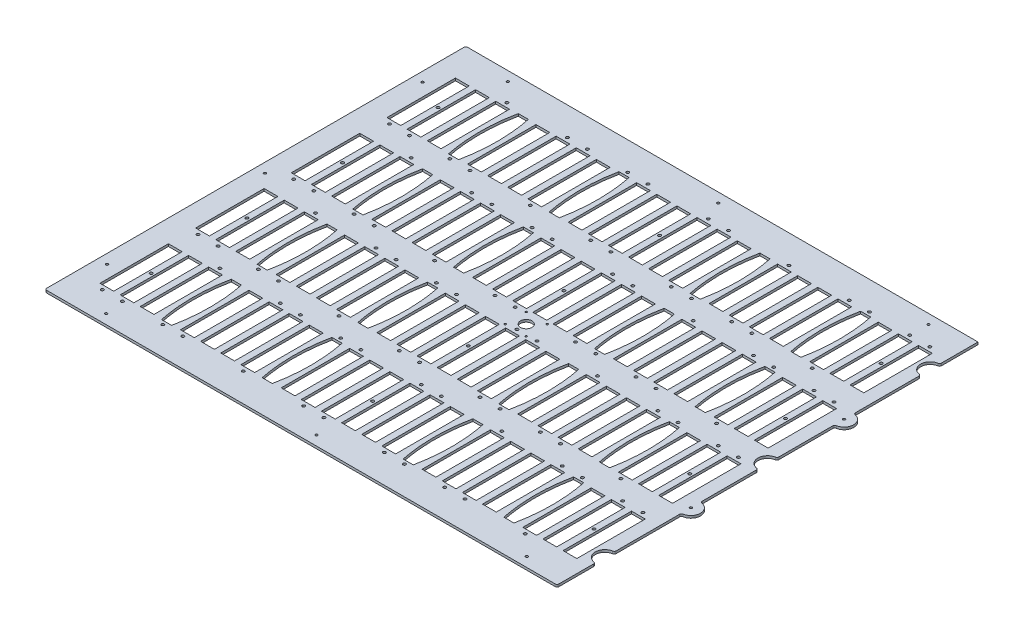
SolidWorks part; units mm, degrees
ref_plane "Front Plane" through (0, 0, 0) normal (0, 0, 1) x (1, 0, 0)
ref_plane "Top Plane" through (0, 0, 0) normal (0, 1, 0) x (1, 0, 0)
ref_plane "Right Plane" through (0, 0, 0) normal (1, 0, 0) x (0, 0, -1)
sketch "Sketch1" plane through (0, 0, 0) normal (0, 1, 0) x (1, 0, 0)
  line L0 (-340.1822, 0) -> (340.1822, 0) construction
  line L1 (-340.1822, -279.5524) -> (340.1822, -279.5524)
  line L2 (-340.1822, -279.5524) -> (-340.1822, 279.5524)
  line L3 (-340.1822, 279.5524) -> (340.1822, 279.5524)
  line L4 (340.1822, -279.5524) -> (340.1822, -228.7524)
  line L5 (-340.1822, -279.5524) -> (340.1822, 279.5524) construction
  line L6 (-340.1822, 279.5524) -> (340.1822, -279.5524) construction
  line L7 (340.1822, -89.0524) -> (340.1822, -12.7)
  line L8 (340.1822, -203.3524) -> (340.1822, -114.4524)
  line L9 (340.1822, 12.7) -> (340.1822, 89.0524)
  line L10 (340.1822, 114.4524) -> (340.1822, 203.3524)
  line L11 (340.1822, 228.7524) -> (340.1822, 279.5524)
  arc A0 (340.1822, 12.7) -> (340.1822, -12.7) centre (340.1822, 0) ccw
  arc A1 (340.1822, -114.4524) -> (340.1822, -89.0524) centre (340.1822, -101.7524) ccw
  arc A2 (340.1822, 89.0524) -> (340.1822, 114.4524) centre (340.1822, 101.7524) ccw
  arc A3 (340.1822, -203.3524) -> (340.1822, -228.7524) centre (340.1822, -216.0524) ccw
  arc A4 (340.1822, 228.7524) -> (340.1822, 203.3524) centre (340.1822, 216.0524) ccw
  point P0 (0, 0)
  dimension "D3" = 63.5
  dimension "D4" = 12.7
  dimension "D5" = 63.5
  dimension "D6" = 177.8
  dimension "D7" = 177.8
  dimension "D1" = 559.1048
  dimension "D2" = 680.3644
extrude "Boss-Extrude1" add sketch "Sketch1" along normal blind 3.175
sketch "Sketch17" plane through (0, 3.175, 0) normal (0, 1, 0) x (1, 0, 0)
  line L0 (340.1822, 279.5524) -> (-340.1822, 279.5524) construction
  line L1 (-314.7822, 254.1524) -> (327.4822, 254.1524) construction
  line L2 (-314.7822, 254.1524) -> (-314.7822, -254.1524) construction
  line L3 (-314.7822, -254.1524) -> (327.4822, -254.1524) construction
  line L4 (327.4822, 254.1524) -> (327.4822, -254.1524) construction
  line L5 (-340.1822, 279.5524) -> (-340.1822, -279.5524) construction
  line L6 (-340.1822, -279.5524) -> (340.1822, -279.5524) construction
  line L7 (340.1822, -203.3524) -> (340.1822, -114.4524) construction
  line L8 (-283.771, 236.1184) -> (-265.483, 236.1184)
  line L9 (-310.515, 236.1184) -> (-292.227, 236.1184)
  line L10 (-310.515, 236.1184) -> (-310.515, 145.1864)
  line L11 (-310.515, 145.1864) -> (-292.227, 145.1864)
  line L12 (-292.227, 236.1184) -> (-292.227, 145.1864)
  line L13 (-283.771, 236.1184) -> (-283.771, 145.1864)
  line L14 (-265.483, 236.1184) -> (-265.483, 145.1864)
  line L15 (-283.771, 145.1864) -> (-265.483, 145.1864)
  line L16 (-257.027, 236.1184) -> (-238.739, 236.1184)
  line L17 (-257.027, 236.1184) -> (-257.027, 145.1864)
  line L18 (-238.739, 236.1184) -> (-238.739, 145.1864)
  line L19 (-257.027, 145.1864) -> (-238.739, 145.1864)
  line L24 (-203.539, 236.1184) -> (-185.251, 236.1184)
  line L25 (-203.539, 236.1184) -> (-203.539, 145.1864)
  line L26 (-185.251, 236.1184) -> (-185.251, 145.1864)
  line L27 (-203.539, 145.1864) -> (-185.251, 145.1864)
  line L28 (-176.795, 236.1184) -> (-158.507, 236.1184)
  line L29 (-176.795, 236.1184) -> (-176.795, 145.1864)
  line L30 (-158.507, 236.1184) -> (-158.507, 145.1864)
  line L31 (-176.795, 145.1864) -> (-158.507, 145.1864)
  line L32 (-150.0511, 236.1184) -> (-131.7631, 236.1184)
  line L33 (-150.0511, 236.1184) -> (-150.0511, 145.1864)
  line L34 (-131.7631, 236.1184) -> (-131.7631, 145.1864)
  line L35 (-150.0511, 145.1864) -> (-131.7631, 145.1864)
  line L36 (-123.3071, 236.1184) -> (-105.0191, 236.1184)
  line L37 (-123.3071, 236.1184) -> (-123.3071, 145.1864)
  line L38 (-105.0191, 236.1184) -> (-105.0191, 145.1864)
  line L39 (-123.3071, 145.1864) -> (-105.0191, 145.1864)
  line L44 (-69.8191, 236.1184) -> (-51.5311, 236.1184)
  line L45 (-69.8191, 236.1184) -> (-69.8191, 145.1864)
  line L46 (-51.5311, 236.1184) -> (-51.5311, 145.1864)
  line L47 (-69.8191, 145.1864) -> (-51.5311, 145.1864)
  line L48 (-43.0751, 236.1184) -> (-24.7871, 236.1184)
  line L49 (-43.0751, 236.1184) -> (-43.0751, 145.1864)
  line L50 (-24.7871, 236.1184) -> (-24.7871, 145.1864)
  line L51 (-43.0751, 145.1864) -> (-24.7871, 145.1864)
  line L52 (-16.3311, 236.1184) -> (1.9569, 236.1184)
  line L53 (-16.3311, 236.1184) -> (-16.3311, 145.1864)
  line L54 (1.9569, 236.1184) -> (1.9569, 145.1864)
  line L55 (-16.3311, 145.1864) -> (1.9569, 145.1864)
  line L56 (10.4129, 236.1184) -> (28.7009, 236.1184)
  line L57 (10.4129, 236.1184) -> (10.4129, 145.1864)
  line L58 (28.7009, 236.1184) -> (28.7009, 145.1864)
  line L59 (10.4129, 145.1864) -> (28.7009, 145.1864)
  line L60 (37.1569, 236.1184) -> (55.4449, 236.1184)
  line L61 (37.1569, 236.1184) -> (37.1569, 145.1864)
  line L62 (55.4449, 236.1184) -> (55.4449, 145.1864)
  line L63 (37.1569, 145.1864) -> (55.4449, 145.1864)
  line L64 (63.9009, 236.1184) -> (82.1889, 236.1184)
  line L65 (63.9009, 236.1184) -> (63.9009, 145.1864)
  line L66 (82.1889, 236.1184) -> (82.1889, 145.1864)
  line L67 (63.9009, 145.1864) -> (82.1889, 145.1864)
  line L72 (117.3889, 236.1184) -> (135.6769, 236.1184)
  line L73 (117.3889, 236.1184) -> (117.3889, 145.1864)
  line L74 (135.6769, 236.1184) -> (135.6769, 145.1864)
  line L75 (117.3889, 145.1864) -> (135.6769, 145.1864)
  line L76 (144.1329, 236.1184) -> (162.4209, 236.1184)
  line L77 (144.1329, 236.1184) -> (144.1329, 145.1864)
  line L78 (162.4209, 236.1184) -> (162.4209, 145.1864)
  line L79 (144.1329, 145.1864) -> (162.4209, 145.1864)
  line L80 (170.8768, 236.1184) -> (189.1648, 236.1184)
  line L81 (170.8768, 236.1184) -> (170.8768, 145.1864)
  line L82 (189.1648, 236.1184) -> (189.1648, 145.1864)
  line L83 (170.8768, 145.1864) -> (189.1648, 145.1864)
  line L84 (197.6208, 236.1184) -> (215.9088, 236.1184)
  line L85 (197.6208, 236.1184) -> (197.6208, 145.1864)
  line L86 (215.9088, 236.1184) -> (215.9088, 145.1864)
  line L87 (197.6208, 145.1864) -> (215.9088, 145.1864)
  line L92 (251.1088, 236.1184) -> (269.3968, 236.1184)
  line L93 (251.1088, 236.1184) -> (251.1088, 145.1864)
  line L94 (269.3968, 236.1184) -> (269.3968, 145.1864)
  line L95 (251.1088, 145.1864) -> (269.3968, 145.1864)
  line L96 (277.8528, 236.1184) -> (296.1408, 236.1184)
  line L97 (277.8528, 236.1184) -> (277.8528, 145.1864)
  line L98 (296.1408, 236.1184) -> (296.1408, 145.1864)
  line L99 (277.8528, 145.1864) -> (296.1408, 145.1864)
  line L100 (304.5968, 236.1184) -> (322.8848, 236.1184)
  line L101 (304.5968, 236.1184) -> (304.5968, 145.1864)
  line L102 (322.8848, 236.1184) -> (322.8848, 145.1864)
  line L103 (304.5968, 145.1864) -> (322.8848, 145.1864)
  line L104 (-283.771, 109.0422) -> (-265.483, 109.0422)
  line L105 (-283.771, 109.0422) -> (-283.771, 18.1102)
  line L106 (-265.483, 109.0422) -> (-265.483, 18.1102)
  line L107 (-283.771, 18.1102) -> (-265.483, 18.1102)
  line L108 (-257.027, 109.0422) -> (-238.739, 109.0422)
  line L109 (-257.027, 109.0422) -> (-257.027, 18.1102)
  line L110 (-238.739, 109.0422) -> (-238.739, 18.1102)
  line L111 (-257.027, 18.1102) -> (-238.739, 18.1102)
  line L116 (-203.539, 109.0422) -> (-185.251, 109.0422)
  line L117 (-203.539, 109.0422) -> (-203.539, 18.1102)
  line L118 (-185.251, 109.0422) -> (-185.251, 18.1102)
  line L119 (-203.539, 18.1102) -> (-185.251, 18.1102)
  line L120 (-176.795, 109.0422) -> (-158.507, 109.0422)
  line L121 (-176.795, 109.0422) -> (-176.795, 18.1102)
  line L122 (-158.507, 109.0422) -> (-158.507, 18.1102)
  line L123 (-176.795, 18.1102) -> (-158.507, 18.1102)
  line L124 (-150.0511, 109.0422) -> (-131.7631, 109.0422)
  line L125 (-150.0511, 109.0422) -> (-150.0511, 18.1102)
  line L126 (-131.7631, 109.0422) -> (-131.7631, 18.1102)
  line L127 (-150.0511, 18.1102) -> (-131.7631, 18.1102)
  line L128 (-123.3071, 109.0422) -> (-105.0191, 109.0422)
  line L129 (-123.3071, 109.0422) -> (-123.3071, 18.1102)
  line L130 (-105.0191, 109.0422) -> (-105.0191, 18.1102)
  line L131 (-123.3071, 18.1102) -> (-105.0191, 18.1102)
  line L136 (-69.8191, 109.0422) -> (-51.5311, 109.0422)
  line L137 (-69.8191, 109.0422) -> (-69.8191, 18.1102)
  line L138 (-51.5311, 109.0422) -> (-51.5311, 18.1102)
  line L139 (-69.8191, 18.1102) -> (-51.5311, 18.1102)
  line L140 (-43.0751, 109.0422) -> (-24.7871, 109.0422)
  line L141 (-43.0751, 109.0422) -> (-43.0751, 18.1102)
  line L142 (-24.7871, 109.0422) -> (-24.7871, 18.1102)
  line L143 (-43.0751, 18.1102) -> (-24.7871, 18.1102)
  line L144 (-16.3311, 109.0422) -> (1.9569, 109.0422)
  line L145 (-16.3311, 109.0422) -> (-16.3311, 18.1102)
  line L146 (1.9569, 109.0422) -> (1.9569, 18.1102)
  line L147 (-16.3311, 18.1102) -> (1.9569, 18.1102)
  line L148 (10.4129, 109.0422) -> (28.7009, 109.0422)
  line L149 (10.4129, 109.0422) -> (10.4129, 18.1102)
  line L150 (28.7009, 109.0422) -> (28.7009, 18.1102)
  line L151 (10.4129, 18.1102) -> (28.7009, 18.1102)
  line L152 (37.1569, 109.0422) -> (55.4449, 109.0422)
  line L153 (37.1569, 109.0422) -> (37.1569, 18.1102)
  line L154 (55.4449, 109.0422) -> (55.4449, 18.1102)
  line L155 (37.1569, 18.1102) -> (55.4449, 18.1102)
  line L156 (63.9009, 109.0422) -> (82.1889, 109.0422)
  line L157 (63.9009, 109.0422) -> (63.9009, 18.1102)
  line L158 (82.1889, 109.0422) -> (82.1889, 18.1102)
  line L159 (63.9009, 18.1102) -> (82.1889, 18.1102)
  line L164 (117.3889, 109.0422) -> (135.6769, 109.0422)
  line L165 (117.3889, 109.0422) -> (117.3889, 18.1102)
  line L166 (135.6769, 109.0422) -> (135.6769, 18.1102)
  line L167 (117.3889, 18.1102) -> (135.6769, 18.1102)
  line L168 (144.1329, 109.0422) -> (162.4209, 109.0422)
  line L169 (144.1329, 109.0422) -> (144.1329, 18.1102)
  line L170 (162.4209, 109.0422) -> (162.4209, 18.1102)
  line L171 (144.1329, 18.1102) -> (162.4209, 18.1102)
  line L172 (170.8768, 109.0422) -> (189.1648, 109.0422)
  line L173 (170.8768, 109.0422) -> (170.8768, 18.1102)
  line L174 (189.1648, 109.0422) -> (189.1648, 18.1102)
  line L175 (170.8768, 18.1102) -> (189.1648, 18.1102)
  line L176 (197.6208, 109.0422) -> (215.9088, 109.0422)
  line L177 (197.6208, 109.0422) -> (197.6208, 18.1102)
  line L178 (215.9088, 109.0422) -> (215.9088, 18.1102)
  line L179 (197.6208, 18.1102) -> (215.9088, 18.1102)
  line L184 (251.1088, 109.0422) -> (269.3968, 109.0422)
  line L185 (251.1088, 109.0422) -> (251.1088, 18.1102)
  line L186 (269.3968, 109.0422) -> (269.3968, 18.1102)
  line L187 (251.1088, 18.1102) -> (269.3968, 18.1102)
  line L188 (277.8528, 109.0422) -> (296.1408, 109.0422)
  line L189 (277.8528, 109.0422) -> (277.8528, 18.1102)
  line L190 (296.1408, 109.0422) -> (296.1408, 18.1102)
  line L191 (277.8528, 18.1102) -> (296.1408, 18.1102)
  line L192 (304.5968, 109.0422) -> (322.8848, 109.0422)
  line L193 (304.5968, 109.0422) -> (304.5968, 18.1102)
  line L194 (322.8848, 109.0422) -> (322.8848, 18.1102)
  line L195 (304.5968, 18.1102) -> (322.8848, 18.1102)
  line L196 (-283.771, -18.034) -> (-265.483, -18.034)
  line L197 (-283.771, -18.034) -> (-283.771, -108.966)
  line L198 (-265.483, -18.034) -> (-265.483, -108.966)
  line L199 (-283.771, -108.966) -> (-265.483, -108.966)
  line L200 (-257.027, -18.034) -> (-238.739, -18.034)
  line L201 (-257.027, -18.034) -> (-257.027, -108.966)
  line L202 (-238.739, -18.034) -> (-238.739, -108.966)
  line L203 (-257.027, -108.966) -> (-238.739, -108.966)
  line L208 (-203.539, -18.034) -> (-185.251, -18.034)
  line L209 (-203.539, -18.034) -> (-203.539, -108.966)
  line L210 (-185.251, -18.034) -> (-185.251, -108.966)
  line L211 (-203.539, -108.966) -> (-185.251, -108.966)
  line L212 (-176.795, -18.034) -> (-158.507, -18.034)
  line L213 (-176.795, -18.034) -> (-176.795, -108.966)
  line L214 (-158.507, -18.034) -> (-158.507, -108.966)
  line L215 (-176.795, -108.966) -> (-158.507, -108.966)
  line L216 (-150.0511, -18.034) -> (-131.7631, -18.034)
  line L217 (-150.0511, -18.034) -> (-150.0511, -108.966)
  line L218 (-131.7631, -18.034) -> (-131.7631, -108.966)
  line L219 (-150.0511, -108.966) -> (-131.7631, -108.966)
  line L220 (-123.3071, -18.034) -> (-105.0191, -18.034)
  line L221 (-123.3071, -18.034) -> (-123.3071, -108.966)
  line L222 (-105.0191, -18.034) -> (-105.0191, -108.966)
  line L223 (-123.3071, -108.966) -> (-105.0191, -108.966)
  line L228 (-69.8191, -18.034) -> (-51.5311, -18.034)
  line L229 (-69.8191, -18.034) -> (-69.8191, -108.966)
  line L230 (-51.5311, -18.034) -> (-51.5311, -108.966)
  line L231 (-69.8191, -108.966) -> (-51.5311, -108.966)
  line L232 (-43.0751, -18.034) -> (-24.7871, -18.034)
  line L233 (-43.0751, -18.034) -> (-43.0751, -108.966)
  line L234 (-24.7871, -18.034) -> (-24.7871, -108.966)
  line L235 (-43.0751, -108.966) -> (-24.7871, -108.966)
  line L236 (-16.3311, -18.034) -> (1.9569, -18.034)
  line L237 (-16.3311, -18.034) -> (-16.3311, -108.966)
  line L238 (1.9569, -18.034) -> (1.9569, -108.966)
  line L239 (-16.3311, -108.966) -> (1.9569, -108.966)
  line L240 (10.4129, -18.034) -> (28.7009, -18.034)
  line L241 (10.4129, -18.034) -> (10.4129, -108.966)
  line L242 (28.7009, -18.034) -> (28.7009, -108.966)
  line L243 (10.4129, -108.966) -> (28.7009, -108.966)
  line L244 (37.1569, -18.034) -> (55.4449, -18.034)
  line L245 (37.1569, -18.034) -> (37.1569, -108.966)
  line L246 (55.4449, -18.034) -> (55.4449, -108.966)
  line L247 (37.1569, -108.966) -> (55.4449, -108.966)
  line L248 (63.9009, -18.034) -> (82.1889, -18.034)
  line L249 (63.9009, -18.034) -> (63.9009, -108.966)
  line L250 (82.1889, -18.034) -> (82.1889, -108.966)
  line L251 (63.9009, -108.966) -> (82.1889, -108.966)
  line L256 (117.3889, -18.034) -> (135.6769, -18.034)
  line L257 (117.3889, -18.034) -> (117.3889, -108.966)
  line L258 (135.6769, -18.034) -> (135.6769, -108.966)
  line L259 (117.3889, -108.966) -> (135.6769, -108.966)
  line L260 (144.1329, -18.034) -> (162.4209, -18.034)
  line L261 (144.1329, -18.034) -> (144.1329, -108.966)
  line L262 (162.4209, -18.034) -> (162.4209, -108.966)
  line L263 (144.1329, -108.966) -> (162.4209, -108.966)
  line L264 (170.8768, -18.034) -> (189.1648, -18.034)
  line L265 (170.8768, -18.034) -> (170.8768, -108.966)
  line L266 (189.1648, -18.034) -> (189.1648, -108.966)
  line L267 (170.8768, -108.966) -> (189.1648, -108.966)
  line L268 (197.6208, -18.034) -> (215.9088, -18.034)
  line L269 (197.6208, -18.034) -> (197.6208, -108.966)
  line L270 (215.9088, -18.034) -> (215.9088, -108.966)
  line L271 (197.6208, -108.966) -> (215.9088, -108.966)
  line L276 (251.1088, -18.034) -> (269.3968, -18.034)
  line L277 (251.1088, -18.034) -> (251.1088, -108.966)
  line L278 (269.3968, -18.034) -> (269.3968, -108.966)
  line L279 (251.1088, -108.966) -> (269.3968, -108.966)
  line L280 (277.8528, -18.034) -> (296.1408, -18.034)
  line L281 (277.8528, -18.034) -> (277.8528, -108.966)
  line L282 (296.1408, -18.034) -> (296.1408, -108.966)
  line L283 (277.8528, -108.966) -> (296.1408, -108.966)
  line L284 (304.5968, -18.034) -> (322.8848, -18.034)
  line L285 (304.5968, -18.034) -> (304.5968, -108.966)
  line L286 (322.8848, -18.034) -> (322.8848, -108.966)
  line L287 (304.5968, -108.966) -> (322.8848, -108.966)
  line L288 (-283.771, -145.1102) -> (-265.483, -145.1102)
  line L289 (-283.771, -145.1102) -> (-283.771, -236.0422)
  line L290 (-265.483, -145.1102) -> (-265.483, -236.0422)
  line L291 (-283.771, -236.0422) -> (-265.483, -236.0422)
  line L292 (-257.027, -145.1102) -> (-238.739, -145.1102)
  line L293 (-257.027, -145.1102) -> (-257.027, -236.0422)
  line L294 (-238.739, -145.1102) -> (-238.739, -236.0422)
  line L295 (-257.027, -236.0422) -> (-238.739, -236.0422)
  line L300 (-203.539, -145.1102) -> (-185.251, -145.1102)
  line L301 (-203.539, -145.1102) -> (-203.539, -236.0422)
  line L302 (-185.251, -145.1102) -> (-185.251, -236.0422)
  line L303 (-203.539, -236.0422) -> (-185.251, -236.0422)
  line L304 (-176.795, -145.1102) -> (-158.507, -145.1102)
  line L305 (-176.795, -145.1102) -> (-176.795, -236.0422)
  line L306 (-158.507, -145.1102) -> (-158.507, -236.0422)
  line L307 (-176.795, -236.0422) -> (-158.507, -236.0422)
  line L308 (-150.0511, -145.1102) -> (-131.7631, -145.1102)
  line L309 (-150.0511, -145.1102) -> (-150.0511, -236.0422)
  line L310 (-131.7631, -145.1102) -> (-131.7631, -236.0422)
  line L311 (-150.0511, -236.0422) -> (-131.7631, -236.0422)
  line L312 (-123.3071, -145.1102) -> (-105.0191, -145.1102)
  line L313 (-123.3071, -145.1102) -> (-123.3071, -236.0422)
  line L314 (-105.0191, -145.1102) -> (-105.0191, -236.0422)
  line L315 (-123.3071, -236.0422) -> (-105.0191, -236.0422)
  line L320 (-69.8191, -145.1102) -> (-51.5311, -145.1102)
  line L321 (-69.8191, -145.1102) -> (-69.8191, -236.0422)
  line L322 (-51.5311, -145.1102) -> (-51.5311, -236.0422)
  line L323 (-69.8191, -236.0422) -> (-51.5311, -236.0422)
  line L324 (-43.0751, -145.1102) -> (-24.7871, -145.1102)
  line L325 (-43.0751, -145.1102) -> (-43.0751, -236.0422)
  line L326 (-24.7871, -145.1102) -> (-24.7871, -236.0422)
  line L327 (-43.0751, -236.0422) -> (-24.7871, -236.0422)
  line L328 (-16.3311, -145.1102) -> (1.9569, -145.1102)
  line L329 (-16.3311, -145.1102) -> (-16.3311, -236.0422)
  line L330 (1.9569, -145.1102) -> (1.9569, -236.0422)
  line L331 (-16.3311, -236.0422) -> (1.9569, -236.0422)
  line L332 (10.4129, -145.1102) -> (28.7009, -145.1102)
  line L333 (10.4129, -145.1102) -> (10.4129, -236.0422)
  line L334 (28.7009, -145.1102) -> (28.7009, -236.0422)
  line L335 (10.4129, -236.0422) -> (28.7009, -236.0422)
  line L336 (37.1569, -145.1102) -> (55.4449, -145.1102)
  line L337 (37.1569, -145.1102) -> (37.1569, -236.0422)
  line L338 (55.4449, -145.1102) -> (55.4449, -236.0422)
  line L339 (37.1569, -236.0422) -> (55.4449, -236.0422)
  line L340 (63.9009, -145.1102) -> (82.1889, -145.1102)
  line L341 (63.9009, -145.1102) -> (63.9009, -236.0422)
  line L342 (82.1889, -145.1102) -> (82.1889, -236.0422)
  line L343 (63.9009, -236.0422) -> (82.1889, -236.0422)
  line L348 (117.3889, -145.1102) -> (135.6769, -145.1102)
  line L349 (117.3889, -145.1102) -> (117.3889, -236.0422)
  line L350 (135.6769, -145.1102) -> (135.6769, -236.0422)
  line L351 (117.3889, -236.0422) -> (135.6769, -236.0422)
  line L352 (144.1329, -145.1102) -> (162.4209, -145.1102)
  line L353 (144.1329, -145.1102) -> (144.1329, -236.0422)
  line L354 (162.4209, -145.1102) -> (162.4209, -236.0422)
  line L355 (144.1329, -236.0422) -> (162.4209, -236.0422)
  line L356 (170.8768, -145.1102) -> (189.1648, -145.1102)
  line L357 (170.8768, -145.1102) -> (170.8768, -236.0422)
  line L358 (189.1648, -145.1102) -> (189.1648, -236.0422)
  line L359 (170.8768, -236.0422) -> (189.1648, -236.0422)
  line L360 (197.6208, -145.1102) -> (215.9088, -145.1102)
  line L361 (197.6208, -145.1102) -> (197.6208, -236.0422)
  line L362 (215.9088, -145.1102) -> (215.9088, -236.0422)
  line L363 (197.6208, -236.0422) -> (215.9088, -236.0422)
  line L368 (251.1088, -145.1102) -> (269.3968, -145.1102)
  line L369 (251.1088, -145.1102) -> (251.1088, -236.0422)
  line L370 (269.3968, -145.1102) -> (269.3968, -236.0422)
  line L371 (251.1088, -236.0422) -> (269.3968, -236.0422)
  line L372 (277.8528, -145.1102) -> (296.1408, -145.1102)
  line L373 (277.8528, -145.1102) -> (277.8528, -236.0422)
  line L374 (296.1408, -145.1102) -> (296.1408, -236.0422)
  line L375 (277.8528, -236.0422) -> (296.1408, -236.0422)
  line L376 (304.5968, -145.1102) -> (322.8848, -145.1102)
  line L377 (304.5968, -145.1102) -> (304.5968, -236.0422)
  line L378 (322.8848, -145.1102) -> (322.8848, -236.0422)
  line L379 (304.5968, -236.0422) -> (322.8848, -236.0422)
  line L380 (-310.515, 109.0422) -> (-292.227, 109.0422)
  line L381 (-310.515, 109.0422) -> (-310.515, 18.1102)
  line L382 (-292.227, 109.0422) -> (-292.227, 18.1102)
  line L383 (-310.515, 18.1102) -> (-292.227, 18.1102)
  line L384 (-310.515, -18.034) -> (-292.227, -18.034)
  line L385 (-310.515, -18.034) -> (-310.515, -108.966)
  line L386 (-292.227, -18.034) -> (-292.227, -108.966)
  line L387 (-310.515, -108.966) -> (-292.227, -108.966)
  line L388 (-310.515, -145.1102) -> (-292.227, -145.1102)
  line L389 (-310.515, -145.1102) -> (-310.515, -236.0422)
  line L390 (-292.227, -145.1102) -> (-292.227, -236.0422)
  line L391 (-310.515, -236.0422) -> (-292.227, -236.0422)
  line L392 (340.1822, -279.5524) -> (340.1822, -228.7524) construction
  line L393 (224.3648, 236.1184) -> (242.6528, 236.1184) [skipped]
  line L394 (224.3648, 236.1184) -> (224.3648, 145.1864) [skipped]
  line L395 (242.6528, 236.1184) -> (242.6528, 145.1864) [skipped]
  line L396 (224.3648, 145.1864) -> (242.6528, 145.1864) [skipped]
  line L397 (224.3648, 109.0422) -> (242.6528, 109.0422) [skipped]
  line L398 (224.3648, 109.0422) -> (224.3648, 18.1102) [skipped]
  line L399 (242.6528, 109.0422) -> (242.6528, 18.1102) [skipped]
  line L400 (224.3648, 18.1102) -> (242.6528, 18.1102) [skipped]
  line L401 (224.3648, -18.034) -> (242.6528, -18.034) [skipped]
  line L402 (224.3648, -18.034) -> (224.3648, -108.966) [skipped]
  line L403 (242.6528, -18.034) -> (242.6528, -108.966) [skipped]
  line L404 (224.3648, -108.966) -> (242.6528, -108.966) [skipped]
  line L405 (224.3648, -145.1102) -> (242.6528, -145.1102) [skipped]
  line L406 (224.3648, -145.1102) -> (224.3648, -236.0422) [skipped]
  line L407 (242.6528, -145.1102) -> (242.6528, -236.0422) [skipped]
  line L408 (224.3648, -236.0422) -> (242.6528, -236.0422) [skipped]
  line L409 (90.6449, 236.1184) -> (108.9329, 236.1184) [skipped]
  line L410 (90.6449, 236.1184) -> (90.6449, 145.1864) [skipped]
  line L411 (108.9329, 236.1184) -> (108.9329, 145.1864) [skipped]
  line L412 (90.6449, 145.1864) -> (108.9329, 145.1864) [skipped]
  line L413 (90.6449, 109.0422) -> (108.9329, 109.0422) [skipped]
  line L414 (90.6449, 109.0422) -> (90.6449, 18.1102) [skipped]
  line L415 (108.9329, 109.0422) -> (108.9329, 18.1102) [skipped]
  line L416 (90.6449, 18.1102) -> (108.9329, 18.1102) [skipped]
  line L417 (90.6449, -18.034) -> (108.9329, -18.034) [skipped]
  line L418 (90.6449, -18.034) -> (90.6449, -108.966) [skipped]
  line L419 (108.9329, -18.034) -> (108.9329, -108.966) [skipped]
  line L420 (90.6449, -108.966) -> (108.9329, -108.966) [skipped]
  line L421 (90.6449, -145.1102) -> (108.9329, -145.1102) [skipped]
  line L422 (90.6449, -145.1102) -> (90.6449, -236.0422) [skipped]
  line L423 (108.9329, -145.1102) -> (108.9329, -236.0422) [skipped]
  line L424 (90.6449, -236.0422) -> (108.9329, -236.0422) [skipped]
  line L425 (-96.5631, 236.1184) -> (-78.2751, 236.1184) [skipped]
  line L426 (-96.5631, 236.1184) -> (-96.5631, 145.1864) [skipped]
  line L427 (-78.2751, 236.1184) -> (-78.2751, 145.1864) [skipped]
  line L428 (-96.5631, 145.1864) -> (-78.2751, 145.1864) [skipped]
  line L429 (-96.5631, 109.0422) -> (-78.2751, 109.0422) [skipped]
  line L430 (-96.5631, 109.0422) -> (-96.5631, 18.1102) [skipped]
  line L431 (-78.2751, 109.0422) -> (-78.2751, 18.1102) [skipped]
  line L432 (-96.5631, 18.1102) -> (-78.2751, 18.1102) [skipped]
  line L433 (-96.5631, -18.034) -> (-78.2751, -18.034) [skipped]
  line L434 (-96.5631, -18.034) -> (-96.5631, -108.966) [skipped]
  line L435 (-78.2751, -18.034) -> (-78.2751, -108.966) [skipped]
  line L436 (-96.5631, -108.966) -> (-78.2751, -108.966) [skipped]
  line L437 (-96.5631, -145.1102) -> (-78.2751, -145.1102) [skipped]
  line L438 (-96.5631, -145.1102) -> (-96.5631, -236.0422) [skipped]
  line L439 (-78.2751, -145.1102) -> (-78.2751, -236.0422) [skipped]
  line L440 (-96.5631, -236.0422) -> (-78.2751, -236.0422) [skipped]
  line L441 (-230.283, 236.1184) -> (-211.995, 236.1184) [skipped]
  line L442 (-230.283, 236.1184) -> (-230.283, 145.1864) [skipped]
  line L443 (-211.995, 236.1184) -> (-211.995, 145.1864) [skipped]
  line L444 (-230.283, 145.1864) -> (-211.995, 145.1864) [skipped]
  line L445 (-230.283, 109.0422) -> (-211.995, 109.0422) [skipped]
  line L446 (-230.283, 109.0422) -> (-230.283, 18.1102) [skipped]
  line L447 (-211.995, 109.0422) -> (-211.995, 18.1102) [skipped]
  line L448 (-230.283, 18.1102) -> (-211.995, 18.1102) [skipped]
  line L449 (-230.283, -18.034) -> (-211.995, -18.034) [skipped]
  line L450 (-230.283, -18.034) -> (-230.283, -108.966) [skipped]
  line L451 (-211.995, -18.034) -> (-211.995, -108.966) [skipped]
  line L452 (-230.283, -108.966) -> (-211.995, -108.966) [skipped]
  line L453 (-230.283, -145.1102) -> (-211.995, -145.1102) [skipped]
  line L454 (-230.283, -145.1102) -> (-230.283, -236.0422) [skipped]
  line L455 (-211.995, -145.1102) -> (-211.995, -236.0422) [skipped]
  line L456 (-230.283, -236.0422) -> (-211.995, -236.0422) [skipped]
  dimension "D1" = 25.4
  dimension "D2" = 25.4
  dimension "D3" = 25.4
  dimension "D4" = 12.7
  dimension "D5" = 18.288
  dimension "D6" = 90.932
  dimension "D7" = 4.2672
  dimension "D8" = 18.034
  dimension "D9" = 508.3048
  dimension "D10" = 642.2644
  dimension "D11" = 24
  dimension "D13" = 17.2974
  dimension "D14" = 43.5102
  dimension "D12" = 4
extrude "Cut-Extrude5" cut sketch "Sketch17" against normal through all
hole_wizard "#25 (0.1495) Diameter Hole1" positions "Sketch18" profile "Sketch19" hole size "#25" standard "ANSI Inch" end condition through all
sketch "Sketch18" plane through (0, 3.175, 0) normal (0, 1, 0) x (1, 0, 0)
  line L19 (340.1822, -241.8842) -> (-340.1822, -241.8842) construction
  line L20 (340.1822, -279.5524) -> (340.1822, -228.7524) construction
  line L21 (-340.1822, 279.5524) -> (-340.1822, -279.5524) construction
  line L22 (340.1822, -139.2682) -> (-340.1822, -139.2682) construction
  line L23 (340.1822, -203.3524) -> (340.1822, -114.4524) construction
  line L24 (313.7408, -236.0422) -> (313.7408, -254.0762) construction
  line L25 (304.5968, -236.0422) -> (322.8848, -236.0422) construction
  line L29 (322.8848, -145.1102) -> (304.5968, -145.1102) construction
  line L30 (313.7408, -241.8842) -> (313.7408, -139.2682) construction
  line L32 (286.9902, -241.8842) -> (286.9902, -139.2682) construction
  line L33 (260.2396, -241.8842) -> (260.2396, -139.2682) construction
  line L34 (233.4889, -241.8842) -> (233.4889, -139.2682) construction
  line L35 (206.7383, -241.8842) -> (206.7383, -139.2682) construction
  line L36 (179.9877, -241.8842) -> (179.9877, -139.2682) construction
  line L37 (153.2371, -241.8842) -> (153.2371, -139.2682) construction
  line L38 (126.4865, -241.8842) -> (126.4865, -139.2682) construction
  line L39 (99.7359, -241.8842) -> (99.7359, -139.2682) construction
  line L40 (72.9852, -241.8842) -> (72.9852, -139.2682) construction
  line L41 (46.2346, -241.8842) -> (46.2346, -139.2682) construction
  line L42 (19.484, -241.8842) -> (19.484, -139.2682) construction
  line L43 (-7.2666, -241.8842) -> (-7.2666, -139.2682) construction
  line L44 (-34.0172, -241.8842) -> (-34.0172, -139.2682) construction
  line L45 (-60.7678, -241.8842) -> (-60.7678, -139.2682) construction
  line L46 (-87.5185, -241.8842) -> (-87.5185, -139.2682) construction
  line L47 (-114.2691, -241.8842) -> (-114.2691, -139.2682) construction
  line L48 (-141.0197, -241.8842) -> (-141.0197, -139.2682) construction
  line L49 (-167.7703, -241.8842) -> (-167.7703, -139.2682) construction
  line L50 (-194.5209, -241.8842) -> (-194.5209, -139.2682) construction
  line L51 (-221.2715, -241.8842) -> (-221.2715, -139.2682) construction
  line L52 (-248.0222, -241.8842) -> (-248.0222, -139.2682) construction
  line L53 (-274.7728, -241.8842) -> (-274.7728, -139.2682) construction
  line L54 (-301.5234, -241.8842) -> (-301.5234, -139.2682) construction
  point P472 (313.7408, -139.2682)
  point P477 (286.9902, -139.2682)
  point P478 (260.2396, -241.8842)
  point P481 (233.4889, -139.2682)
  point P483 (206.7383, -139.2682)
  point P484 (179.9877, -241.8842)
  point P486 (153.2371, -241.8842)
  point P489 (126.4865, -139.2682)
  point P490 (99.7359, -241.8842)
  point P492 (72.9852, -241.8842)
  point P495 (46.2346, -139.2682)
  point P497 (19.484, -139.2682)
  point P498 (-7.2666, -241.8842)
  point P500 (-34.0172, -241.8842)
  point P503 (-60.7678, -139.2682)
  point P505 (-87.5185, -139.2682)
  point P506 (-114.2691, -241.8842)
  point P509 (-141.0197, -139.2682)
  point P511 (-167.7703, -139.2682)
  point P512 (-194.5209, -241.8842)
  point P514 (-221.2715, -241.8842)
  point P517 (-248.0222, -139.2682)
  point P518 (-274.7728, -241.8842)
  point P520 (-301.5234, -241.8842)
  point P575 (313.7408, -12.192)
  point P576 (286.9902, -12.192)
  point P577 (260.2396, -114.808)
  point P578 (233.4889, -12.192)
  point P579 (206.7383, -12.192)
  point P580 (179.9877, -114.808)
  point P581 (153.2371, -114.808)
  point P582 (126.4865, -12.192)
  point P583 (99.7359, -114.808)
  point P584 (72.9852, -114.808)
  point P585 (46.2346, -12.192)
  point P586 (19.484, -12.192)
  point P587 (-7.2666, -114.808)
  point P588 (-34.0172, -114.808)
  point P589 (-60.7678, -12.192)
  point P590 (-87.5185, -12.192)
  point P591 (-114.2691, -114.808)
  point P592 (-141.0197, -12.192)
  point P593 (-167.7703, -12.192)
  point P594 (-194.5209, -114.808)
  point P595 (-221.2715, -114.808)
  point P596 (-248.0222, -12.192)
  point P597 (-274.7728, -114.808)
  point P598 (-301.5234, -114.808)
  point P599 (313.7408, 114.8842)
  point P600 (286.9902, 114.8842)
  point P601 (260.2396, 12.2682)
  point P602 (233.4889, 114.8842)
  point P603 (206.7383, 114.8842)
  point P604 (179.9877, 12.2682)
  point P605 (153.2371, 12.2682)
  point P606 (126.4865, 114.8842)
  point P607 (99.7359, 12.2682)
  point P608 (72.9852, 12.2682)
  point P609 (46.2346, 114.8842)
  point P610 (19.484, 114.8842)
  point P611 (-7.2666, 12.2682)
  point P612 (-34.0172, 12.2682)
  point P613 (-60.7678, 114.8842)
  point P614 (-87.5185, 114.8842)
  point P615 (-114.2691, 12.2682)
  point P616 (-141.0197, 114.8842)
  point P617 (-167.7703, 114.8842)
  point P618 (-194.5209, 12.2682)
  point P619 (-221.2715, 12.2682)
  point P620 (-248.0222, 114.8842)
  point P621 (-274.7728, 12.2682)
  point P622 (-301.5234, 12.2682)
  point P623 (313.7408, 241.9604)
  point P624 (286.9902, 241.9604)
  point P625 (260.2396, 139.3444)
  point P626 (233.4889, 241.9604)
  point P627 (206.7383, 241.9604)
  point P628 (179.9877, 139.3444)
  point P629 (153.2371, 139.3444)
  point P630 (126.4865, 241.9604)
  point P631 (99.7359, 139.3444)
  point P632 (72.9852, 139.3444)
  point P633 (46.2346, 241.9604)
  point P634 (19.484, 241.9604)
  point P635 (-7.2666, 139.3444)
  point P636 (-34.0172, 139.3444)
  point P637 (-60.7678, 241.9604)
  point P638 (-87.5185, 241.9604)
  point P639 (-114.2691, 139.3444)
  point P640 (-141.0197, 241.9604)
  point P641 (-167.7703, 241.9604)
  point P642 (-194.5209, 139.3444)
  point P643 (-221.2715, 139.3444)
  point P644 (-248.0222, 241.9604)
  point P645 (-274.7728, 139.3444)
  point P646 (-301.5234, 139.3444)
  dimension "D1" = 5.842
  dimension "D2" = 5.842
  dimension "D3" = 24
  dimension "D4" = 4
sketch "Sketch19" plane through (-301.5234, 3.175, -139.3444) normal (1, 0, 0) x (0, 0, 1)
  line L0 (0, 0) -> (0, 3.175)
  line L1 (0, 3.175) -> (1.8986, 3.175)
  line L2 (1.8986, 3.175) -> (1.8986, 0)
  line L5 (1.8986, 0) -> (0, 0)
  line L11 (0, -6.35) -> (0, 107.95) construction
  dimension "Thru Hole Dia." = 3.7973
  dimension "Thru Hole Depth" = 3.175
fillet "Fillet1" radius 2.54 13 edges at (-340.1822, 1.5875, -279.5524) (-340.1822, 1.5875, 279.5524) (340.1822, 1.5875, 279.5524) (340.1822, 1.5875, 203.3524) (340.1822, 1.5875, 228.7524) (340.1822, 1.5875, -228.7524) (340.1822, 1.5875, -203.3524) (340.1822, 1.5875, -114.4524) (340.1822, 1.5875, -89.0524) (340.1822, 1.5875, -12.7) (340.1822, 1.5875, 12.7) (340.1822, 1.5875, 89.0524) (340.1822, 1.5875, 114.4524)
hole_wizard "#6 Clearance Hole1" positions "Sketch8" profile "Sketch9" hole size "#6" standard "ANSI Inch" end condition through all
sketch "Sketch8" plane through (0, 3.175, 0) normal (0, 1, 0) x (1, 0, 0)
  line L13 (-292.227, 236.1184) -> (-283.771, 145.1864) construction
  line L15 (1.9569, 236.1184) -> (10.4129, 145.1864) construction
  line L17 (296.1408, 236.1184) -> (304.5968, 145.1864) construction
  line L18 (-292.227, 109.0422) -> (-283.771, 18.1102) construction
  line L19 (1.9569, 109.0422) -> (10.4129, 18.1102) construction
  line L20 (296.1408, 109.0422) -> (304.5968, 18.1102) construction
  line L21 (-292.227, -18.034) -> (-283.771, -108.966) construction
  line L22 (1.9569, -18.034) -> (10.4129, -108.966) construction
  line L23 (296.1408, -18.034) -> (304.5968, -108.966) construction
  line L24 (-292.227, -145.1102) -> (-283.771, -236.0422) construction
  line L25 (1.9569, -145.1102) -> (10.4129, -236.0422) construction
  line L26 (296.1408, -145.1102) -> (304.5968, -236.0422) construction
  point P129 (-287.999, 190.6524)
  point P131 (6.1849, 190.6524)
  point P133 (300.3688, 190.6524)
  point P146 (-287.999, 63.5762)
  point P147 (6.1849, 63.5762)
  point P148 (300.3688, 63.5762)
  point P155 (-287.999, -63.5)
  point P156 (6.1849, -63.5)
  point P157 (300.3688, -63.5)
  point P164 (-287.999, -190.5762)
  point P165 (6.1849, -190.5762)
  point P166 (300.3688, -190.5762)
  dimension "D1" = 4
sketch "Sketch9" plane through (300.3688, 3.175, 190.5762) normal (1, 0, 0) x (0, 0, 1)
  line L0 (0, 0) -> (0, 3.175)
  line L1 (0, 3.175) -> (1.8986, 3.175)
  line L2 (1.8986, 3.175) -> (1.8986, 0)
  line L5 (1.8986, 0) -> (0, 0)
  line L11 (0, -6.35) -> (0, 107.95) construction
  dimension "Thru Hole Dia." = 3.7973
  dimension "Thru Hole Depth" = 3.175
hole_wizard "#2 Clearance Hole1" positions "Sketch13" profile "Sketch14" hole size "#2" standard "ANSI Inch" end condition through all
sketch "Sketch13" plane through (0, 3.175, 0) normal (0, 1, 0) x (1, 0, 0)
  line L9 (322.8848, -108.966) -> (322.8848, -18.034) construction
  line L10 (322.8848, -18.034) -> (304.5968, -18.034) construction
  line L18 (10.4129, 18.1102) -> (28.7009, -18.034) construction
  line L21 (5.6261, -13.9319) -> (33.5661, -13.9319) construction
  line L22 (5.6261, -13.9319) -> (5.6261, 14.0081) construction
  line L23 (5.6261, 14.0081) -> (33.5661, 14.0081) construction
  line L24 (33.5661, -13.9319) -> (33.5661, 14.0081) construction
  line L25 (5.6261, -13.9319) -> (33.5661, 14.0081) construction
  line L26 (5.6261, 14.0081) -> (33.5661, -13.9319) construction
  line L27 (10.4129, 18.1102) -> (28.7009, 18.1102) construction
  point P129 (5.6261, 14.0081)
  point P132 (5.6261, -13.9319)
  point P135 (33.5661, -13.9319)
  point P138 (33.5661, 14.0081)
  dimension "D1" = 27.94
  dimension "D2" = 27.94
  dimension "D3" = 4.1021
sketch "Sketch14" plane through (33.5661, 3.175, -14.0081) normal (1, 0, 0) x (0, 0, 1)
  line L0 (0, 0) -> (0, 3.175)
  line L1 (0, 3.175) -> (1.2192, 3.175)
  line L2 (1.2192, 3.175) -> (1.2192, 0)
  line L5 (1.2192, 0) -> (0, 0)
  line L11 (0, -6.35) -> (0, 107.95) construction
  dimension "Thru Hole Dia." = 2.4384
  dimension "Thru Hole Depth" = 3.175
sketch "Sketch20" plane through (0, 3.175, 0) normal (0, 1, 0) x (1, 0, 0)
  line L0 (5.6261, 14.0081) -> (33.5661, -13.9319) construction
  circle A0 centre (19.5961, 0.0381) radius 7.62
  dimension "D1" = 15.24
extrude "Cut-Extrude6" cut sketch "Sketch20" against normal through all
hole_wizard "1/8 (0.125) Diameter Hole1" positions "Sketch21" profile "Sketch22" hole size "1/8" standard "ANSI Inch" end condition through all
sketch "Sketch21" plane through (0, 3.175, 0) normal (0, 1, 0) x (1, 0, 0)
  point P0 (287.274, -266.8524)
  point P12 (287.274, 266.8524)
  point P15 (7.874, 266.8524)
  point P18 (-271.526, 266.8524)
  point P21 (-327.5584, 209.55)
  point P24 (-327.5584, 0)
  point P27 (-327.5584, -209.55)
  point P30 (-271.526, -266.8524)
  point P33 (7.874, -266.8524)
  point P56 (340.1822, 101.7524)
  point P59 (340.1822, -101.7524)
sketch "Sketch22" plane through (287.274, 3.175, 266.8524) normal (1, 0, 0) x (0, 0, 1)
  line L0 (0, 0) -> (0, 3.175)
  line L1 (0, 3.175) -> (1.5875, 3.175)
  line L2 (1.5875, 3.175) -> (1.5875, 0)
  line L5 (1.5875, 0) -> (0, 0)
  line L11 (0, -6.35) -> (0, 107.95) construction
  dimension "Thru Hole Dia." = 3.175
  dimension "Thru Hole Depth" = 3.175
sketch "Sketch23" plane through (0, 3.175, 0) normal (0, 1, 0) x (1, 0, 0)
  line L0 (251.1088, -236.0422) -> (215.9088, -145.1102) construction
  line L1 (244.9388, -190.5762) -> (222.0788, -190.5762) construction
  line L2 (240.2398, -144.2212) -> (226.7778, -144.2212)
  line L3 (240.2398, -144.2212) -> (240.2398, -236.9312) construction
  line L4 (240.2398, -236.9312) -> (226.7778, -236.9312)
  line L5 (226.7778, -144.2212) -> (226.7778, -236.9312) construction
  line L6 (240.2398, -144.2212) -> (226.7778, -236.9312) construction
  line L7 (240.2398, -236.9312) -> (226.7778, -144.2212) construction
  line L8 (106.5033, -236.9312) -> (93.0413, -236.9312)
  line L9 (106.5033, -144.2212) -> (93.0413, -144.2212)
  line L10 (-80.7278, -236.9312) -> (-94.1898, -236.9312)
  line L11 (-80.7278, -144.2212) -> (-94.1898, -144.2212)
  line L12 (-214.4643, -236.9312) -> (-227.9263, -236.9312)
  line L13 (-214.4643, -144.2212) -> (-227.9263, -144.2212)
  line L14 (240.2398, -109.855) -> (226.7778, -109.855)
  line L15 (240.2398, -17.145) -> (226.7778, -17.145)
  line L16 (106.5033, -109.855) -> (93.0413, -109.855)
  line L17 (106.5033, -17.145) -> (93.0413, -17.145)
  line L18 (-80.7278, -109.855) -> (-94.1898, -109.855)
  line L19 (-80.7278, -17.145) -> (-94.1898, -17.145)
  line L20 (-214.4643, -109.855) -> (-227.9263, -109.855)
  line L21 (-214.4643, -17.145) -> (-227.9263, -17.145)
  line L22 (240.2398, 17.2212) -> (226.7778, 17.2212)
  line L23 (240.2398, 109.9312) -> (226.7778, 109.9312)
  line L24 (106.5033, 17.2212) -> (93.0413, 17.2212)
  line L25 (106.5033, 109.9312) -> (93.0413, 109.9312)
  line L26 (-80.7278, 17.2212) -> (-94.1898, 17.2212)
  line L27 (-80.7278, 109.9312) -> (-94.1898, 109.9312)
  line L28 (-214.4643, 17.2212) -> (-227.9263, 17.2212)
  line L29 (-214.4643, 109.9312) -> (-227.9263, 109.9312)
  line L30 (240.2398, 144.2974) -> (226.7778, 144.2974)
  line L31 (240.2398, 237.0074) -> (226.7778, 237.0074)
  line L32 (106.5033, 144.2974) -> (93.0413, 144.2974)
  line L33 (106.5033, 237.0074) -> (93.0413, 237.0074)
  line L34 (-80.7278, 144.2974) -> (-94.1898, 144.2974)
  line L35 (-80.7278, 237.0074) -> (-94.1898, 237.0074)
  line L36 (-214.4643, 144.2974) -> (-227.9263, 144.2974)
  line L37 (-214.4643, 237.0074) -> (-227.9263, 237.0074)
  line L38 (322.8848, -108.966) -> (322.8848, -18.034) construction
  line L39 (322.8848, -18.034) -> (304.5968, -18.034) construction
  spline S0 degree 2 poles (226.7778, -236.9312) (217.3798, -190.5762) (226.7778, -144.2212) knots 0 0 0 1 1 1
  spline S1 degree 2 poles (240.2398, -236.9312) (249.6378, -190.5762) (240.2398, -144.2212) knots 0 0 0 1 1 1
  spline S2 degree 2 poles (106.5033, -236.9312) (115.9013, -190.5762) (106.5033, -144.2212) knots 0 0 0 1 1 1
  spline S3 degree 2 poles (93.0413, -236.9312) (83.6433, -190.5762) (93.0413, -144.2212) knots 0 0 0 1 1 1
  spline S4 degree 2 poles (-80.7278, -236.9312) (-71.3298, -190.5762) (-80.7278, -144.2212) knots 0 0 0 1 1 1
  spline S5 degree 2 poles (-94.1898, -236.9312) (-103.5878, -190.5762) (-94.1898, -144.2212) knots 0 0 0 1 1 1
  spline S6 degree 2 poles (-214.4643, -236.9312) (-205.0663, -190.5762) (-214.4643, -144.2212) knots 0 0 0 1 1 1
  spline S7 degree 2 poles (-227.9263, -236.9312) (-237.3243, -190.5762) (-227.9263, -144.2212) knots 0 0 0 1 1 1
  spline S8 degree 2 poles (240.2398, -109.855) (249.6378, -63.5) (240.2398, -17.145) knots 0 0 0 1 1 1
  spline S9 degree 2 poles (106.5033, -109.855) (115.9013, -63.5) (106.5033, -17.145) knots 0 0 0 1 1 1
  spline S10 degree 2 poles (93.0413, -109.855) (83.6433, -63.5) (93.0413, -17.145) knots 0 0 0 1 1 1
  spline S11 degree 2 poles (226.7778, -109.855) (217.3798, -63.5) (226.7778, -17.145) knots 0 0 0 1 1 1
  spline S12 degree 2 poles (-80.7278, -109.855) (-71.3298, -63.5) (-80.7278, -17.145) knots 0 0 0 1 1 1
  spline S13 degree 2 poles (-94.1898, -109.855) (-103.5878, -63.5) (-94.1898, -17.145) knots 0 0 0 1 1 1
  spline S14 degree 2 poles (-214.4643, -109.855) (-205.0663, -63.5) (-214.4643, -17.145) knots 0 0 0 1 1 1
  spline S15 degree 2 poles (-227.9263, -109.855) (-237.3243, -63.5) (-227.9263, -17.145) knots 0 0 0 1 1 1
  spline S16 degree 2 poles (240.2398, 17.2212) (249.6378, 63.5762) (240.2398, 109.9312) knots 0 0 0 1 1 1
  spline S17 degree 2 poles (106.5033, 17.2212) (115.9013, 63.5762) (106.5033, 109.9312) knots 0 0 0 1 1 1
  spline S18 degree 2 poles (93.0413, 17.2212) (83.6433, 63.5762) (93.0413, 109.9312) knots 0 0 0 1 1 1
  spline S19 degree 2 poles (226.7778, 17.2212) (217.3798, 63.5762) (226.7778, 109.9312) knots 0 0 0 1 1 1
  spline S20 degree 2 poles (-80.7278, 17.2212) (-71.3298, 63.5762) (-80.7278, 109.9312) knots 0 0 0 1 1 1
  spline S21 degree 2 poles (-94.1898, 17.2212) (-103.5878, 63.5762) (-94.1898, 109.9312) knots 0 0 0 1 1 1
  spline S22 degree 2 poles (-214.4643, 17.2212) (-205.0663, 63.5762) (-214.4643, 109.9312) knots 0 0 0 1 1 1
  spline S23 degree 2 poles (-227.9263, 17.2212) (-237.3243, 63.5762) (-227.9263, 109.9312) knots 0 0 0 1 1 1
  spline S24 degree 2 poles (240.2398, 144.2974) (249.6378, 190.6524) (240.2398, 237.0074) knots 0 0 0 1 1 1
  spline S25 degree 2 poles (106.5033, 144.2974) (115.9013, 190.6524) (106.5033, 237.0074) knots 0 0 0 1 1 1
  spline S26 degree 2 poles (93.0413, 144.2974) (83.6433, 190.6524) (93.0413, 237.0074) knots 0 0 0 1 1 1
  spline S27 degree 2 poles (226.7778, 144.2974) (217.3798, 190.6524) (226.7778, 237.0074) knots 0 0 0 1 1 1
  spline S28 degree 2 poles (-80.7278, 144.2974) (-71.3298, 190.6524) (-80.7278, 237.0074) knots 0 0 0 1 1 1
  spline S29 degree 2 poles (-94.1898, 144.2974) (-103.5878, 190.6524) (-94.1898, 237.0074) knots 0 0 0 1 1 1
  spline S30 degree 2 poles (-214.4643, 144.2974) (-205.0663, 190.6524) (-214.4643, 237.0074) knots 0 0 0 1 1 1
  spline S31 degree 2 poles (-227.9263, 144.2974) (-237.3243, 190.6524) (-227.9263, 237.0074) knots 0 0 0 1 1 1
  point P4 (233.5088, -190.5762)
  point P12 (233.5088, -190.5762)
  dimension "D1" = 92.71
  dimension "D2" = 13.462
  dimension "D3" = 22.86
  dimension "D7" = 211.6825
  dimension "D8" = 216.3815
  dimension "D9" = 403.6126
  dimension "D10" = 234.5425
  dimension "D11" = 398.9136
  dimension "D12" = 0.889
  dimension "D14" = 421.7736
  dimension "D15" = 532.6501
  dimension "D16" = 81.6102
  dimension "D17" = 208.6864
  dimension "D18" = 555.5101
  dimension "D19" = 45.466
  dimension "D4" = 2
  dimension "D5" = 2
  dimension "D6" = 4
extrude "Cut-Extrude7" cut sketch "Sketch23" against normal through all
